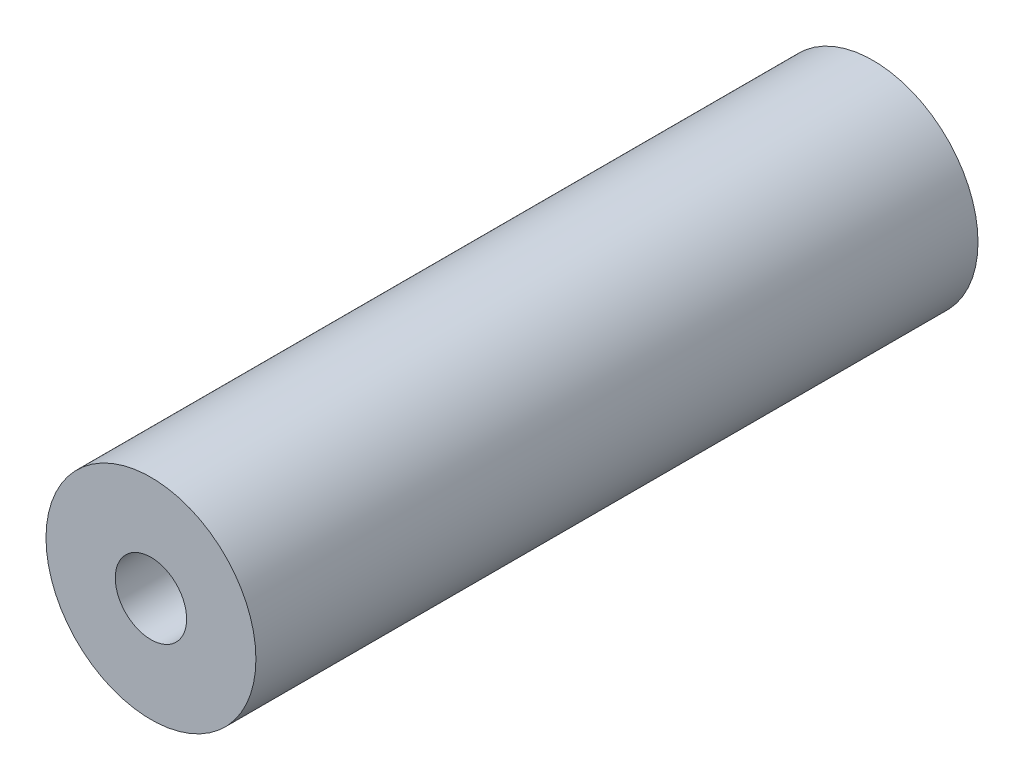
SolidWorks part; units mm, degrees
material "AISI 1020"
ref_plane "Спереди" through (0, 0, 0) normal (0, 0, 1) x (1, 0, 0)
ref_plane "Сверху" through (0, 0, 0) normal (0, 1, 0) x (1, 0, 0)
ref_plane "Справа" through (0, 0, 0) normal (1, 0, 0) x (0, 0, -1)
sketch "Эскиз2" plane through (0, 0, 0) normal (1, 0, 0) x (0, 0, -1)
  line L0 (23, 12.5) -> (23, 0) construction
  line L1 (0, 0) -> (43, 0)
  line L2 (0, 0) -> (0, 12.5)
  line L3 (0, 12.5) -> (43, 12.5)
  line L4 (43, 0) -> (43, 12.5)
  line L5 (20, -230.3984) -> (20, 198.7465) construction
  line L15 (18.5, 12.5) -> (6.5, 12.5) construction
  dimension "D1" = 3
  dimension "D2" = 20
revolve "Повернуть1" add sketch "Эскиз2" angle 360 about L1
hole_wizard "Отверстие обработанное метчиком M101" positions "Эскиз3" profile "Эскиз4" tap size "M10" standard "ISO"
sketch "Эскиз3" plane through (0, 0, -43) normal (0, 0, -1) x (-1, 0, 0)
  point P0 (0, 0)
sketch "Эскиз4" plane through (0, 0, -43) normal (1, 0, 0) x (0, 1, 0)
  line L0 (0, 0) -> (0, 30.0537)
  line L1 (0, 30.0537) -> (4.25, 27.5)
  line L2 (4.25, 27.5) -> (4.25, 0)
  line L5 (4.25, 0) -> (0, 0)
  line L10 (0, 30.0537) -> (-4.25, 27.5) construction
  line L11 (0, -6.35) -> (0, 107.95) construction
  dimension "Диаметр сверла" = 8.5
  dimension "Глубина сверла" = 27.5
  dimension "Угол заточки сверла" = 118
cosmetic thread "Отверстие резьбы3" parameters "D1"=0, "D2"=9.5
mirror "Зеркальное отражение1" about plane through (0, 0, 0) normal (0, 0, -1) of bodies 104
